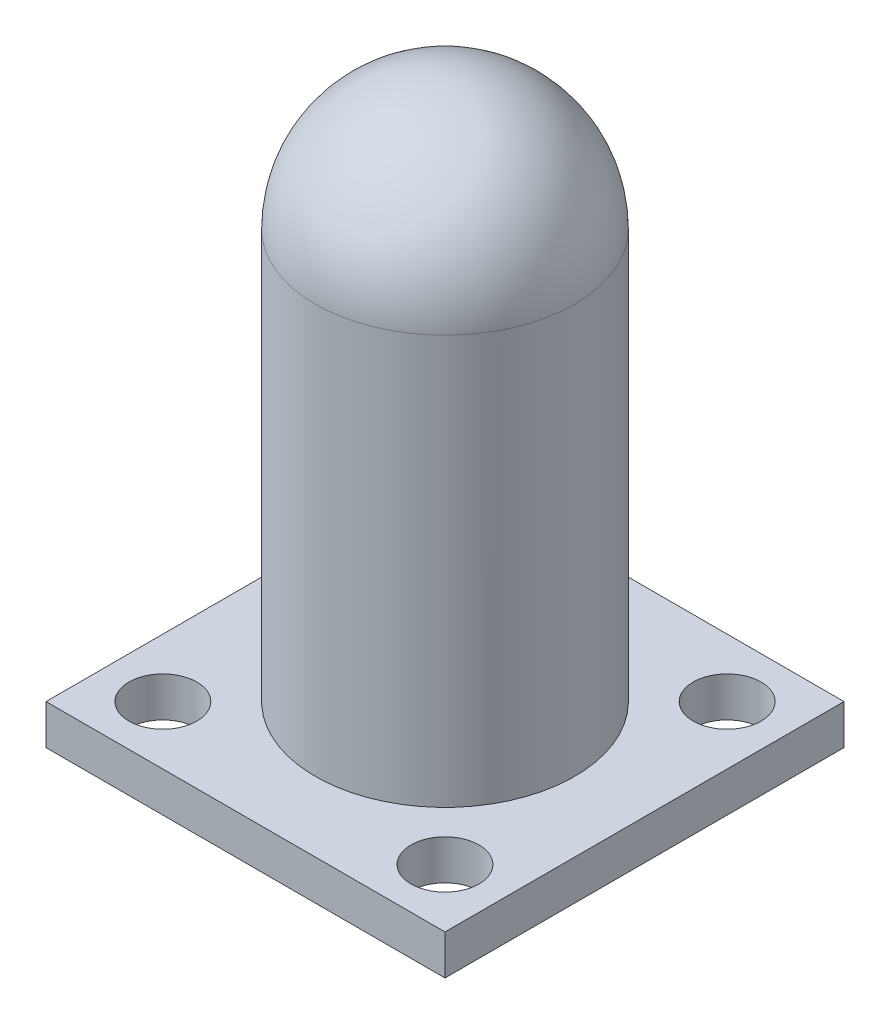
SolidWorks part; units mm, degrees
ref_plane "Plan de face" through (0, 0, 0) normal (0, 0, 1) x (1, 0, 0)
ref_plane "Plan de dessus" through (0, 0, 0) normal (0, 1, 0) x (1, 0, 0)
ref_plane "Plan de droite" through (0, 0, 0) normal (1, 0, 0) x (0, 0, -1)
sketch "Esquisse2" plane through (0, 0, 0) normal (0, 0, 1) x (1, 0, 0)
  line L0 (0, 0) -> (0, 53.633) construction
  line L1 (0, 53.633) -> (0, 56.5828) construction
  line L2 (6.5, 0) -> (6.5, 20.5)
  line L3 (4, 0) -> (4, 20.5)
  line L4 (4, 0) -> (6.5, 0)
  line L5 (6.5, 20.5) -> (-8.2011, 20.5) construction
  line L6 (0, 27) -> (0, 25.9443)
  line L7 (0, 0) -> (34.7739, 0) construction
  line L8 (0, 27) -> (0, 24.5)
  arc A0 (4, 20.5) -> (0, 24.5) centre (0, 20.5) ccw
  arc A1 (6.5, 20.5) -> (0, 27) centre (0, 20.5) ccw
  dimension "D2" = 27
  dimension "D1" = 2.5
  dimension "D3" = 4
revolve "Révolution3" add sketch "Esquisse2" angle 360 about L0
sketch "Esquisse3" plane through (0, 0, 0) normal (0, -1, 0) x (1, 0, 0)
  line L1 (-10, -10) -> (10, -10)
  line L2 (-10, -10) -> (-10, 10)
  line L3 (-10, 10) -> (10, 10)
  line L4 (10, -10) -> (10, 10)
  line L5 (-10, -10) -> (10, 10) construction
  line L6 (-10, 10) -> (10, -10) construction
  point P0 (0, 0)
  dimension "D1" = 20
extrude "Boss.-Extru.1" add sketch "Esquisse3" along normal blind 2
sketch "Esquisse4" plane through (0, 0, 0) normal (0, 1, 0) x (1, 0, 0)
  line L1 (7.0711, -7.0711) -> (-7.0711, -7.0711)
  line L2 (7.0711, -7.0711) -> (7.0711, 7.0711)
  line L3 (7.0711, 7.0711) -> (-7.0711, 7.0711)
  line L4 (-7.0711, -7.0711) -> (-7.0711, 7.0711)
  line L5 (7.0711, -7.0711) -> (-7.0711, 7.0711) construction
  line L6 (7.0711, 7.0711) -> (-7.0711, -7.0711) construction
  point P0 (0, 0)
  dimension "D1" = 10
hole_wizard "Dégagement M31" positions "Esquisse6" profile "Esquisse5" hole size "M3" standard "Iso"
sketch "Esquisse6" plane through (0, 0, 0) normal (0, 1, 0) x (1, 0, 0)
  point P0 (-7.0711, 7.0711)
  point P3 (7.0711, 7.0711)
  point P6 (7.0711, -7.0711)
  point P9 (-7.0711, -7.0711)
sketch "Esquisse5" plane through (-7.0711, 0, -7.0711) normal (1, 0, 0) x (0, 0, 1)
  line L0 (0, 0) -> (0, 4.0215)
  line L1 (0, 4.0215) -> (1.7, 3)
  line L2 (1.7, 3) -> (1.7, 0)
  line L5 (1.7, 0) -> (0, 0)
  line L10 (0, 4.0215) -> (-1.7, 3) construction
  line L11 (0, -6.35) -> (0, 107.95) construction
  dimension "Diamètre du perçage" = 3.4
  dimension "Profondeur du perçage" = 3
  dimension "Angle de pointe" = 118
